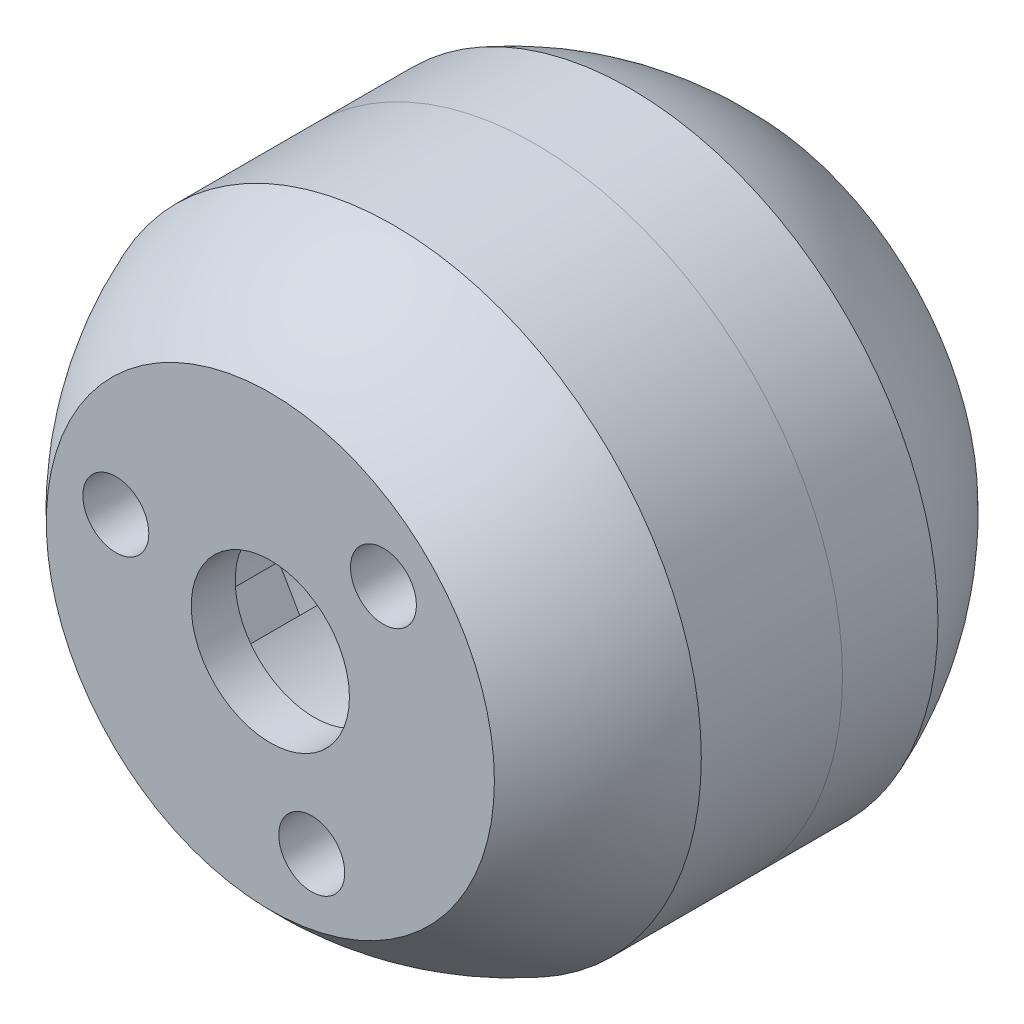
SolidWorks part; units mm, degrees
material "PLA/ABS"
ref_plane "Front Plane" through (0, 0, 0) normal (0, 0, 1) x (1, 0, 0)
ref_plane "Top Plane" through (0, 0, 0) normal (0, 1, 0) x (1, 0, 0)
ref_plane "Right Plane" through (0, 0, 0) normal (1, 0, 0) x (0, 0, -1)
other "Bounding Box"
ref_plane "Default Plane" through (-8.9266, -12.7485, 0) normal (-0.1736, 0.9848, 0) x (0.9848, 0.1736, 0)
sketch "Sketch1" plane through (0, 0, 0) normal (1, 0, 0) x (0, 0, -1)
  line L0 (-34.925, 0) -> (-34.925, 32.3788)
  line L1 (34.925, 0) -> (34.925, 32.3788)
  line L2 (-34.925, 0) -> (0, 0)
  line L3 (0, 0) -> (34.925, 0)
  line L4 (-17.0979, 44.45) -> (17.0979, 44.45)
  line L5 (-3.175, 41.275) -> (3.175, 41.275) construction
  line L6 (-3.175, 41.275) -> (-3.175, -41.275) construction
  line L7 (-3.175, -41.275) -> (3.175, -41.275) construction
  line L8 (3.175, 41.275) -> (3.175, -41.275) construction
  line L9 (-3.175, 41.275) -> (3.175, -41.275) construction
  line L10 (-3.175, -41.275) -> (3.175, 41.275) construction
  circle A1 centre (0, 0) radius 44.45 construction
  arc A2 (-17.0979, 44.45) -> (17.0979, 44.45) centre (0, 0) ccw construction
  arc A4 (34.925, 32.3788) -> (17.0979, 44.45) centre (0, 0) ccw
  arc A5 (-17.0979, 44.45) -> (-34.925, 32.3788) centre (0, 0) ccw
  dimension "D1" = 88.9
  dimension "D5" = 95.25
  dimension "D2" = 6.35
  dimension "D3" = 82.55
  dimension "D4" = 31.75
revolve "Revolve2" add sketch "Sketch1" angle 360 about L2
sketch "Sketch2" plane through (0, 0, 0) normal (0, 0, 1) x (1, 0, 0)
  circle A0 centre (0, 0) radius 41.275 construction
  circle A1 centre (0, 0) radius 41.4782
  dimension "D1" = 0.2032
extrude "Cut-Extrude1" cut sketch "Sketch2" against normal mid plane 6.604
sketch "Sketch3" plane through (0, 0, 0) normal (0, 0, 1) x (1, 0, 0)
  line L0 (0, 0) -> (-38.4948, -22.225) construction
  line L1 (0, 0) -> (-22.3264, 5.9823) construction
  line L2 (-16.3441, 16.3441) -> (0, 0) construction
  line L3 (0, 0) -> (0, 44.45) construction
  circle A1 centre (0, 0) radius 44.45 construction
  circle A2 centre (-22.3264, 5.9823) radius 4.7625
  circle A3 centre (-16.3441, 16.3441) radius 4.7625 construction
  point P11 (-7.7008, 20.6576)
  point P12 (-22.2228, 3.3842)
  dimension "D5" = 9.525
  dimension "D1" = 120
  dimension "D2" = 45
  dimension "D3" = 45
  dimension "D4" = 23.114
extrude "Cut-Extrude2" cut sketch "Sketch3" along normal through all
sketch "Sketch4" plane through (0, 0, 0) normal (0, 0, 1) x (1, 0, 0)
  circle A0 centre (-16.3441, 16.3441) radius 4.7625 construction
  circle A1 centre (-16.3441, 16.3441) radius 4.7625
extrude "Cut-Extrude3" cut sketch "Sketch4" against normal through all
sketch "Sketch6" plane through (0, 0, 0) normal (0, 0, 1) x (1, 0, 0)
  line L0 (0, 0) -> (0, 18.415) construction
  line L1 (-8.5725, 35.56) -> (8.5725, 35.56) construction
  line L2 (-8.5725, 35.56) -> (-8.5725, 18.415) construction
  line L3 (-8.5725, 18.415) -> (8.5725, 18.415) construction
  line L4 (8.5725, 35.56) -> (8.5725, 18.415) construction
  line L5 (-8.5725, 35.56) -> (8.5725, 18.415) construction
  line L6 (-8.5725, 18.415) -> (8.5725, 35.56) construction
  line L7 (-9.2075, 17.78) -> (9.2075, 17.78)
  line L8 (9.2075, 36.195) -> (9.2075, 17.78)
  line L9 (-9.2075, 36.195) -> (9.2075, 36.195)
  line L10 (-9.2075, 36.195) -> (-9.2075, 17.78)
  point P0 (0, 26.9875)
  dimension "D1" = 18.415
  dimension "D2" = 17.145
  dimension "D3" = 0.635
extrude "Cut-Extrude5" cut sketch "Sketch6" against normal mid plane 57.785
pattern_circular "CirPattern1" count 3 over 360 about axis through (0, 0, 0) along (0, 0, 1) of "Cut-Extrude3", "Cut-Extrude2", "Cut-Extrude5"
sketch "Sketch5" plane through (0, 0, 0) normal (0, 0, 1) x (1, 0, 0)
  circle A0 centre (0, 0) radius 18.034
  dimension "D1" = 36.068
extrude "Cut-Extrude4" cut sketch "Sketch5" against normal through all from offset 28.575
sketch "Sketch7" plane through (0, 0, 34.925) normal (0, 0, 1) x (1, 0, 0)
  circle A0 centre (0, 0) radius 11.43
  dimension "D1" = 22.86
extrude "Cut-Extrude6" cut sketch "Sketch7" against normal through all
ref_plane "Plane1" through (0, 0, -3.302) normal (0, 0, 1) x (1, 0, 0)
split "Split1" trim tools "Plane1" bodies to split 113 resulting bodies 105 106
